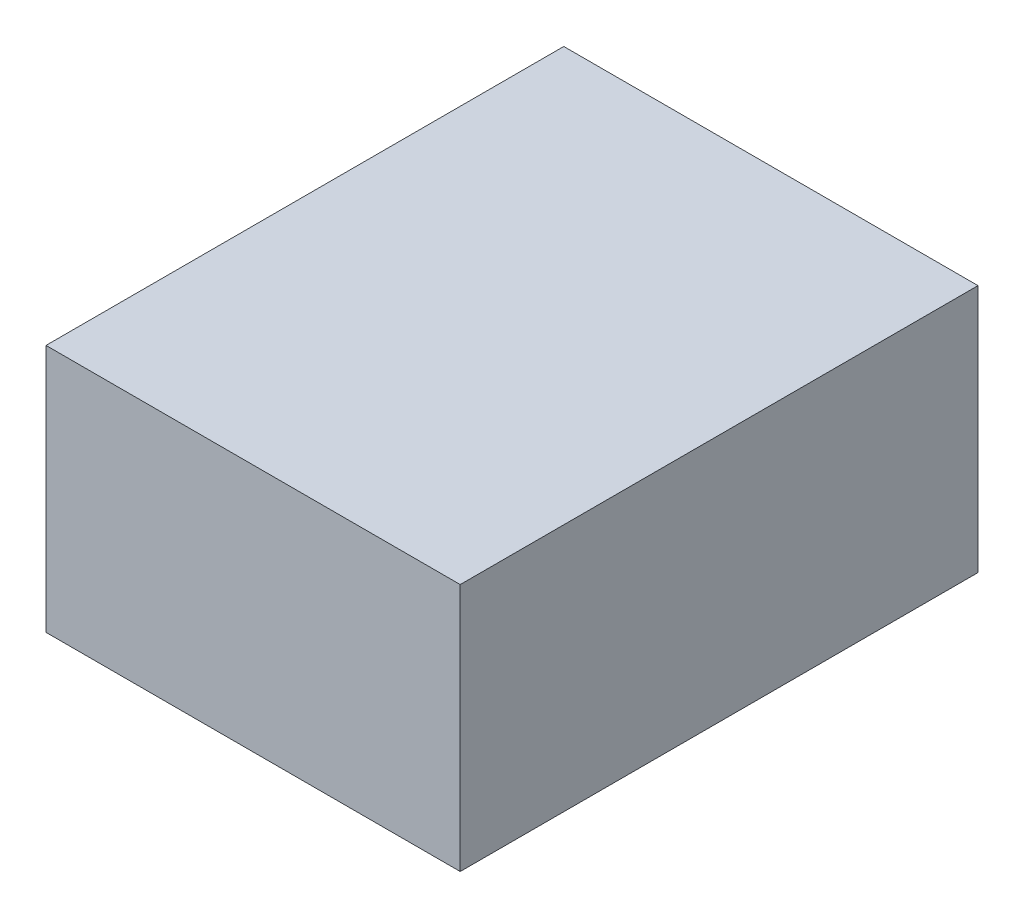
SolidWorks part; units mm, degrees
ref_plane "Front Plane" through (0, 0, 0) normal (0, 0, 1) x (1, 0, 0)
ref_plane "Top Plane" through (0, 0, 0) normal (0, 1, 0) x (1, 0, 0)
ref_plane "Right Plane" through (0, 0, 0) normal (1, 0, 0) x (0, 0, -1)
sketch "BaseS" plane through (0, 0, 0) normal (0, 1, 0) x (1, 0, 0)
  line L1 (-1, 1.25) -> (1, 1.25)
  line L2 (-1, 1.25) -> (-1, -1.25)
  line L3 (-1, -1.25) -> (1, -1.25)
  line L4 (1, 1.25) -> (1, -1.25)
  line L5 (-1, 1.25) -> (1, -1.25) construction
  line L6 (-1, -1.25) -> (1, 1.25) construction
  point P0 (0, 0)
  dimension "Width" = 2
  dimension "Length" = 2.5
extrude "Base" add sketch "BaseS" along normal blind 1.2
